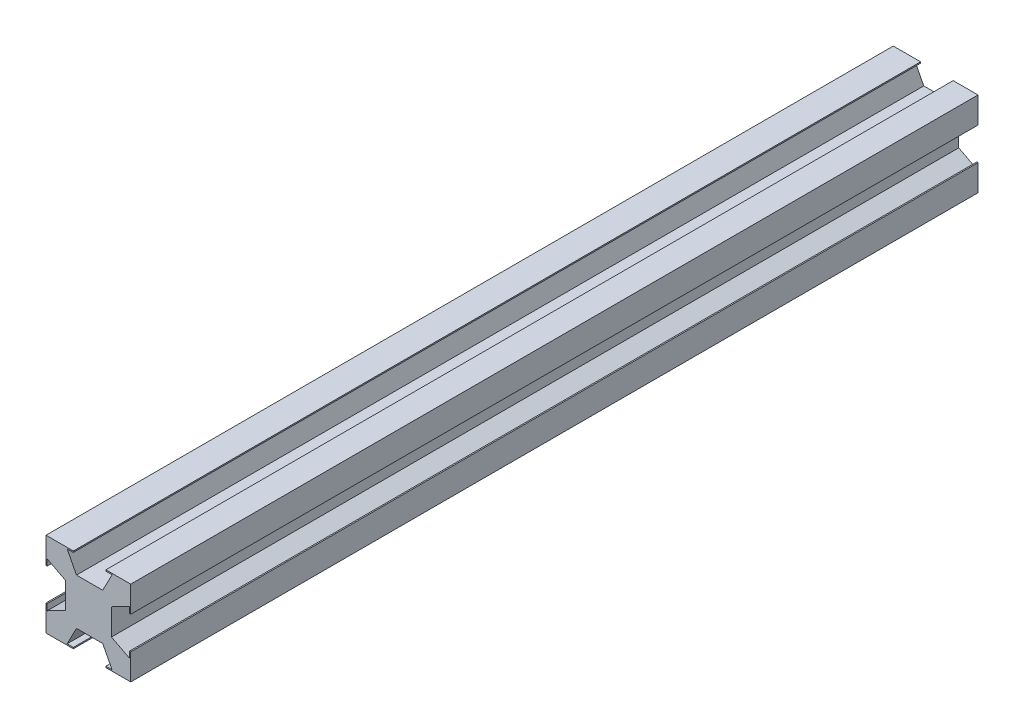
SolidWorks part; units mm, degrees
ref_plane "Ön Düzlem" through (0, 0, 0) normal (0, 0, 1) x (1, 0, 0)
ref_plane "Üst Düzlem" through (0, 0, 0) normal (0, 1, 0) x (1, 0, 0)
ref_plane "Sağ Düzlem" through (0, 0, 0) normal (1, 0, 0) x (0, 0, -1)
sketch "Çizim1" plane through (0, 0, 0) normal (0, 0, 1) x (1, 0, 0)
  line L0 (-5.1576, 10) -> (-2.803, 5.445)
  line L1 (-10, 10) -> (-5.1576, 10)
  line L2 (-10, 10) -> (-10, 5.45)
  line L3 (-10, -10) -> (-5.1576, -10)
  line L4 (10, 10) -> (10, 5.45)
  line L5 (-10, 10) -> (10, -10) construction
  line L6 (-10, -10) -> (10, 10) construction
  line L7 (-2.803, 5.445) -> (3.3917, 5.445)
  line L8 (10, 5.45) -> (5.4451, 3.095)
  line L9 (5.7462, 10) -> (3.3917, 5.445)
  line L10 (5.7462, 10) -> (10, 10)
  line L11 (5.4451, 3.095) -> (5.4451, -3.095)
  line L12 (5.7462, -10) -> (3.3917, -5.445)
  line L13 (-2.803, -5.445) -> (3.3917, -5.445)
  line L14 (-5.1576, -10) -> (-2.803, -5.445)
  line L15 (5.7462, -10) -> (10, -10)
  line L16 (5.4451, -3.095) -> (10, -5.45)
  line L17 (0, 2.2406) -> (0, -12.6593) construction
  line L18 (-5.4451, -3.095) -> (-10, -5.45)
  line L19 (-5.4451, 3.095) -> (-5.4451, -3.095)
  line L20 (-10, 5.45) -> (-5.4451, 3.095)
  line L21 (-10, -5.45) -> (-10, -10)
  line L22 (10, -5.45) -> (10, -10)
  point P0 (0, 0)
  point P12 (0.2943, 5.445)
  dimension "D1" = 20
  dimension "D2" = 20
  dimension "D3" = 6.19
  dimension "D4" = 4.55
  dimension "D5" = 4.55
  dimension "D6" = 117.34
  dimension "D7" = 117.34
extrude "Yükseklik-Ekstrüzyon1" add sketch "Çizim1" along normal blind 200
sketch "Çizim4" plane through (0, 0, 200) normal (0, 0, 1) x (1, 0, 0)
  line L0 (-5.1576, 10) -> (-3.55, 10)
  line L1 (-3.55, 10) -> (-3.55, 9.7051)
  line L2 (-3.55, 9.7051) -> (-5.0052, 9.7051)
  line L3 (-2.803, 5.445) -> (-5.1576, 10) construction
  line L4 (-5.0052, 9.7051) -> (-5.1576, 10)
  line L6 (10, 3.84) -> (9.71, 3.84)
  line L7 (5.5938, 9.7051) -> (5.7462, 10)
  line L8 (4.1386, 9.7051) -> (5.5938, 9.7051)
  line L9 (4.1386, 10) -> (4.1386, 9.7051)
  line L10 (5.7462, 10) -> (4.1386, 10)
  line L11 (-6.9605, 0) -> (11.3985, 0) construction
  line L12 (5.7462, -10) -> (4.1386, -10)
  line L13 (4.1386, -10) -> (4.1386, -9.7051)
  line L14 (4.1386, -9.7051) -> (5.5938, -9.7051)
  line L15 (5.5938, -9.7051) -> (5.7462, -10)
  line L16 (-5.0052, -9.7051) -> (-5.1576, -10)
  line L17 (-3.55, -9.7051) -> (-5.0052, -9.7051)
  line L18 (-3.55, -10) -> (-3.55, -9.7051)
  line L19 (-5.1576, -10) -> (-3.55, -10)
  line L20 (-10, 5.45) -> (-10, 3.84)
  line L21 (-10, 3.84) -> (-9.71, 3.84)
  line L22 (-9.71, 3.84) -> (-9.71, 5.3001)
  line L23 (-10, 5.45) -> (-5.4451, 3.095) construction
  line L24 (-9.71, 5.3001) -> (-10, 5.45)
  line L25 (10, 5.45) -> (10, 3.84)
  line L26 (9.71, 3.84) -> (9.71, 5.3001)
  line L27 (5.4451, 3.095) -> (10, 5.45) construction
  line L28 (9.71, 5.3001) -> (10, 5.45)
  line L29 (9.71, -5.3001) -> (10, -5.45)
  line L30 (9.71, -3.84) -> (9.71, -5.3001)
  line L31 (10, -5.45) -> (10, -3.84)
  line L32 (10, -3.84) -> (9.71, -3.84)
  line L33 (-9.71, -5.3001) -> (-10, -5.45)
  line L34 (-9.71, -3.84) -> (-9.71, -5.3001)
  line L35 (-10, -3.84) -> (-9.71, -3.84)
  line L36 (-10, -5.45) -> (-10, -3.84)
  point P11 (0.2943, 5.445)
  dimension "D1" = 1.6076
  dimension "D2" = 1.61
  dimension "D3" = 0.29
  dimension "D4" = 0.29
  dimension "D5" = 1.61
extrude "Yükseklik-Ekstrüzyon3" add sketch "Çizim4" against normal up to surface (200 mm away) up to face at (0.1177, 0, 0)
